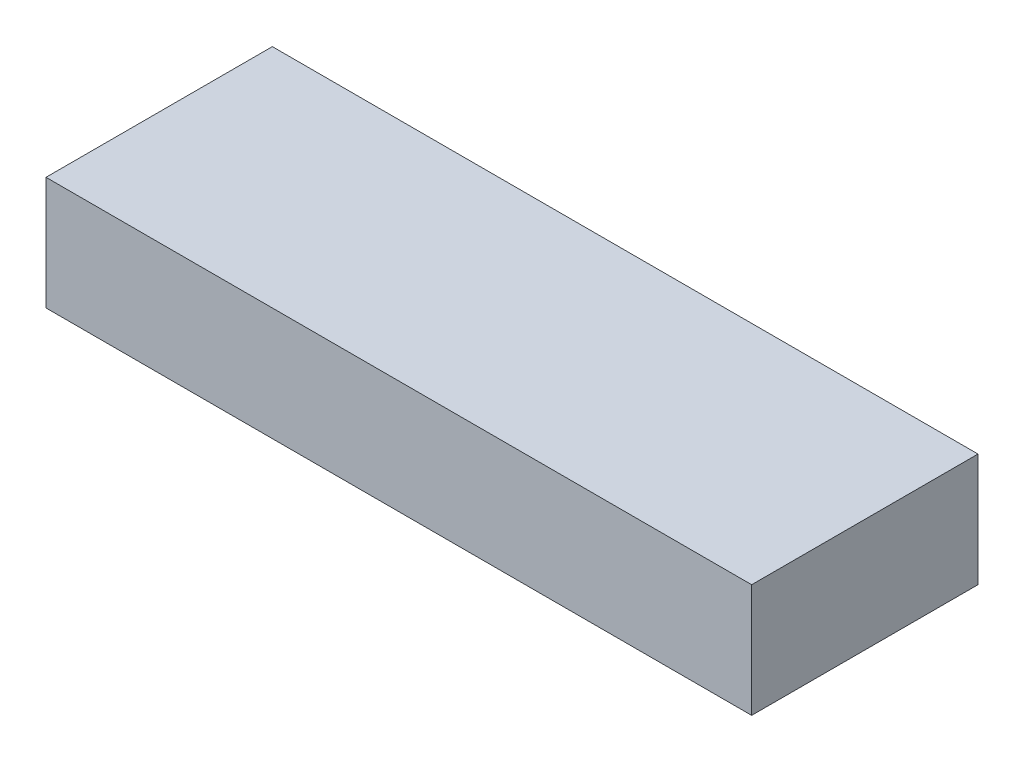
SolidWorks part; units mm, degrees
ref_plane "Front Plane" through (0, 0, 0) normal (0, 0, 1) x (1, 0, 0)
ref_plane "Top Plane" through (0, 0, 0) normal (0, 1, 0) x (1, 0, 0)
ref_plane "Right Plane" through (0, 0, 0) normal (1, 0, 0) x (0, 0, -1)
sketch "Sketch1" plane through (0, 0, 0) normal (0, 1, 0) x (1, 0, 0)
  line L0 (-53, 17) -> (53, -17) construction
  line L1 (-53, 17) -> (53, 17)
  line L2 (-53, 17) -> (-53, -17)
  line L3 (-53, -17) -> (53, -17)
  line L4 (53, 17) -> (53, -17)
  line L5 (53, 17) -> (-53, -17) construction
  point P4 (0, 0)
  dimension "D1" = 106
  dimension "D2" = 34
extrude "Boss-Extrude1" add sketch "Sketch1" along normal blind 17
